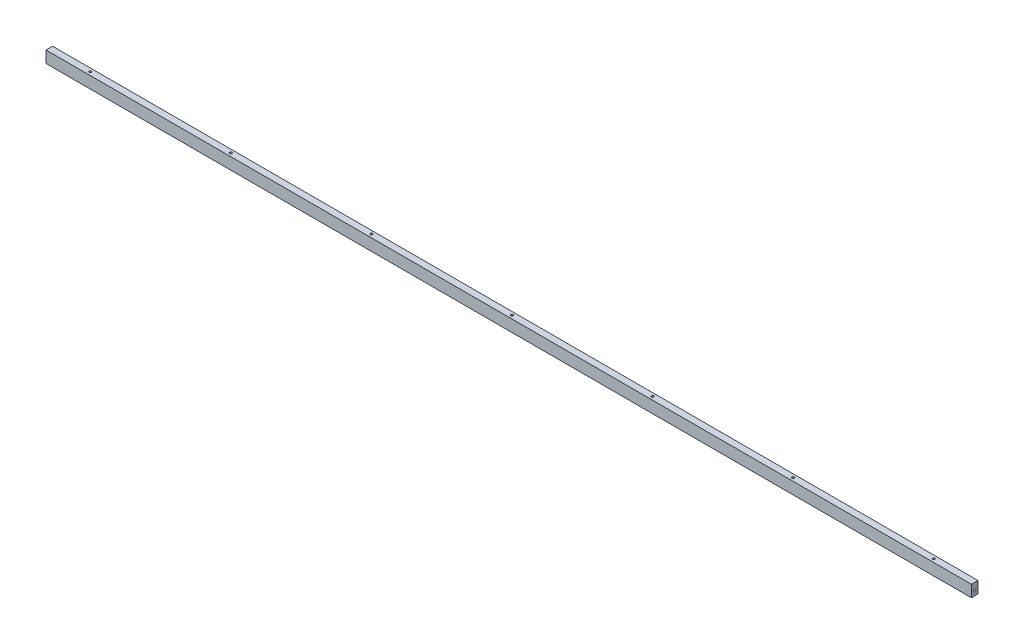
SolidWorks part; units mm, degrees
material "A3钢"
ref_plane "前视基准面" through (0, 0, 0) normal (0, 0, 1) x (1, 0, 0)
ref_plane "上视基准面" through (0, 0, 0) normal (0, 1, 0) x (1, 0, 0)
ref_plane "右视基准面" through (0, 0, 0) normal (1, 0, 0) x (0, 0, -1)
sketch "草图1" plane through (0, 0, 0) normal (0, 0, 1) x (1, 0, 0)
  line L1 (-987.5, -12.5) -> (987.5, -12.5)
  line L2 (-987.5, -12.5) -> (-987.5, 12.5)
  line L3 (-987.5, 12.5) -> (987.5, 12.5)
  line L4 (987.5, -12.5) -> (987.5, 12.5)
  line L5 (-987.5, -12.5) -> (987.5, 12.5) construction
  line L6 (-987.5, 12.5) -> (987.5, -12.5) construction
  point P0 (0, 0)
  dimension "D1" = 1975
  dimension "D2" = 25
extrude "凸台-拉伸1" add sketch "草图1" along normal mid plane 14
sketch "草图2" plane through (0, 0, 7) normal (0, 0, 1) x (1, 0, 0)
  line L0 (0, 619.8775) -> (0, -680.849) construction
  line L1 (-987.5, 12.5) -> (-987.5, -12.5) construction
  line L2 (-980, -90) -> (980, -90)
  line L3 (-980, -90) -> (-980, 90)
  line L4 (-980, 90) -> (980, 90)
  line L5 (980, -90) -> (980, 90)
  line L6 (-980, -90) -> (980, 90) construction
  line L7 (-980, 90) -> (980, -90) construction
  line L8 (-980, 0) -> (1266.3795, 0) construction
  point P3 (0, 0)
  dimension "D1" = 7.5
  dimension "D2" = 180
sketch "草图3" plane through (0, 12.5, 0) normal (0, 1, 0) x (1, 0, 0)
  line L0 (0, 7) -> (0, -7) construction
  line L1 (987.5, 7) -> (-987.5, 7) construction
  line L2 (987.5, -7) -> (-987.5, -7) construction
  line L3 (0, 0) -> (-300, 0) construction
  line L4 (-300, 0) -> (-600, 0) construction
  line L5 (-600, 0) -> (-900, 0) construction
  line L6 (600, 0) -> (900, 0) construction
  line L7 (300, 0) -> (600, 0) construction
  dimension "D1" = 300
hole_wizard "M6 螺纹孔1" positions "3D草图1" profile "草图4" tap size "M6" standard "GB"
sketch3d "3D草图1"
  point P0 (-900, 12.5, 0)
  point P3 (-600, 12.5, 0)
  point P6 (-300, 12.5, 0)
  point P9 (900, 12.5, 0)
  point P12 (600, 12.5, 0)
  point P15 (300, 12.5, 0)
  point P18 (0, 12.5, 0)
sketch "草图4" plane through (-900, 12.5, 0) normal (1, 0, 0) x (0, 0, 1)
  line L0 (0, 0) -> (0, 16.5022)
  line L1 (0, 16.5022) -> (2.5, 15)
  line L2 (2.5, 15) -> (2.5, 0)
  line L5 (2.5, 0) -> (0, 0)
  line L10 (0, 16.5022) -> (-2.5, 15) construction
  line L11 (0, -6.35) -> (0, 107.95) construction
  dimension "螺纹孔钻头直径" = 5
  dimension "螺纹孔钻头深度" = 15
  dimension "导头角度" = 118
cosmetic thread "孔螺蚊线1" parameters "D1"=12, "D2"=6
cosmetic thread "孔螺蚊线2" parameters "D1"=12, "D2"=6
cosmetic thread "孔螺蚊线3" parameters "D1"=12, "D2"=6
cosmetic thread "孔螺蚊线4" parameters "D1"=12, "D2"=6
cosmetic thread "孔螺蚊线5" parameters "D1"=12, "D2"=6
cosmetic thread "孔螺蚊线6" parameters "D1"=12, "D2"=6
cosmetic thread "孔螺蚊线7" parameters "D1"=12, "D2"=6
sketch "草图5" plane through (987.5, 0, 0) normal (1, 0, 0) x (0, 0, -1)
  line L0 (0, 12.5) -> (0, -2.5) construction
  line L1 (-7, 12.5) -> (7, 12.5) construction
  dimension "D1" = 15
hole_wizard "M6 螺纹孔2" positions "3D草图2" profile "草图6" tap size "M6" standard "GB"
sketch3d "3D草图2"
  point P0 (987.5, -2.5, 0)
sketch "草图6" plane through (987.5, -2.5, 0) normal (0, 1, 0) x (0, 0, -1)
  line L0 (0, 0) -> (0, 16.5022)
  line L1 (0, 16.5022) -> (2.5, 15)
  line L2 (2.5, 15) -> (2.5, 0)
  line L5 (2.5, 0) -> (0, 0)
  line L10 (0, 16.5022) -> (-2.5, 15) construction
  line L11 (0, -6.35) -> (0, 107.95) construction
  dimension "螺纹孔钻头直径" = 5
  dimension "螺纹孔钻头深度" = 15
  dimension "导头角度" = 118
cosmetic thread "孔螺蚊线8" parameters "D1"=12, "D2"=6
mirror "镜向1" about plane through (0, 0, 0) normal (1, 0, 0) of "M6 螺纹孔2"
mirror "镜向2" about plane through (0, 0, 0) normal (1, 0, 0) of "镜向1"
